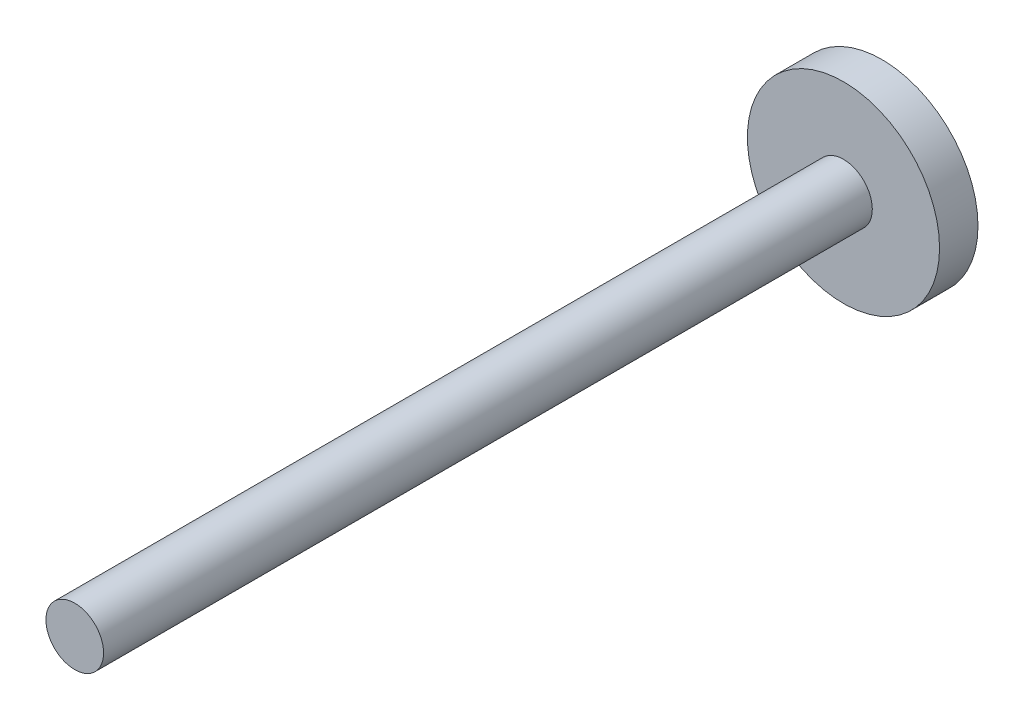
SolidWorks part; units mm, degrees
ref_plane "Front Plane" through (0, 0, 0) normal (0, 0, 1) x (1, 0, 0)
ref_plane "Top Plane" through (0, 0, 0) normal (0, 1, 0) x (1, 0, 0)
ref_plane "Right Plane" through (0, 0, 0) normal (1, 0, 0) x (0, 0, -1)
sketch "Sketch1" plane through (0, 0, 0) normal (0, 0, 1) x (1, 0, 0)
  circle A0 centre (0, 0) radius 10
extrude "Boss-Extrude1" add sketch "Sketch1" along normal blind 4
sketch "Sketch2" plane through (0, 0, 4) normal (0, 0, 1) x (1, 0, 0)
  circle A0 centre (0, 0) radius 3
extrude "Boss-Extrude2" add sketch "Sketch2" along normal blind 80
sketch "Sketch3" plane through (0, 0, 0) normal (0, 0, -1) x (-1, 0, 0)
  line L1 (-4.1484, 7.0971) -> (-8.2204, -0.0441)
  line L2 (-8.2204, -0.0441) -> (-4.072, -7.1411)
  line L3 (-4.072, -7.1411) -> (4.1484, -7.0971)
  line L4 (4.1484, -7.0971) -> (8.2204, 0.0441)
  line L5 (8.2204, 0.0441) -> (4.072, 7.1411)
  line L6 (4.072, 7.1411) -> (-4.1484, 7.0971)
  circle A0 centre (0, 0) radius 7.1192 construction
extrude "Cut-Extrude1" cut sketch "Sketch3" against normal blind 2
